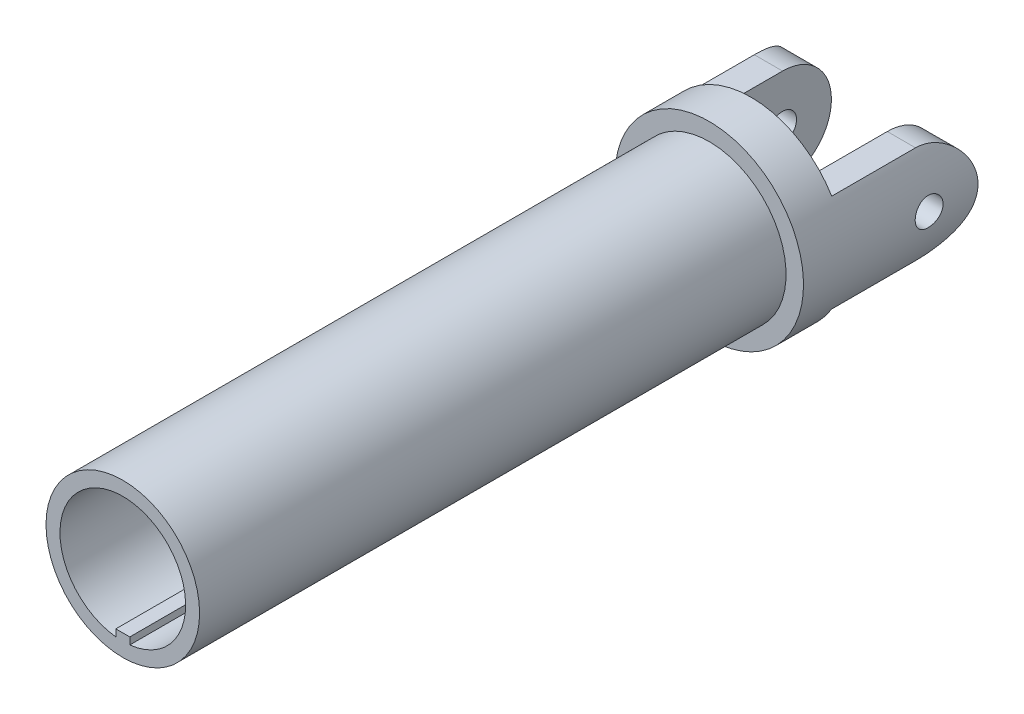
SolidWorks part; units mm, degrees
ref_plane "Front Plane" through (0, 0, 0) normal (0, 0, 1) x (1, 0, 0)
ref_plane "Top Plane" through (0, 0, 0) normal (0, 1, 0) x (1, 0, 0)
ref_plane "Right Plane" through (0, 0, 0) normal (1, 0, 0) x (0, 0, -1)
sketch "Sketch1" plane through (0, 0, 0) normal (0, 0, 1) x (1, 0, 0)
  circle A0 centre (0, 0) radius 5.5
  dimension "D1" = 11
extrude "Yoke" add sketch "Sketch1" along normal mid plane 42 contours A0
sketch "Sketch2" plane through (0, 0, -21) normal (0, 0, -1) x (-1, 0, 0)
  circle A0 centre (0, 0) radius 6.75
  dimension "D1" = 13.5
extrude "U Joint Base" add sketch "Sketch2" along normal blind 3
sketch "Sketch3" plane through (0, 0, -24) normal (0, 0, -1) x (-1, 0, 0)
  line L0 (-5.7717, 3.5) -> (-3.75, 3.5)
  line L1 (-3.75, 3.5) -> (-3.75, -3.5)
  line L2 (-3.75, -3.5) -> (-5.7717, -3.5)
  line L3 (3.75, -3.5) -> (3.75, 3.5)
  line L4 (3.75, 3.5) -> (5.7717, 3.5)
  line L5 (5.7717, -3.5) -> (3.75, -3.5)
  circle A0 centre (0, 0) radius 6.75 construction
  arc A1 (-5.7717, -3.5) -> (-5.7717, 3.5) centre (0, 0) cw
  arc A2 (5.7717, 3.5) -> (5.7717, -3.5) centre (0, 0) cw
  point P16 (0, 0)
  dimension "D2" = 7.5
  dimension "D3" = 7
  dimension "D1" = 2
extrude "U Joint Standups" add sketch "Sketch3" along normal blind 9.5
sketch "Sketch4" plane through (0, 0, 0) normal (1, 0, 0) x (0, 0, -1)
  line L0 (33.5, 3.5) -> (24, 3.5) construction
  line L1 (33.5, -3.5) -> (33.5, 3.5) construction
  line L2 (30, -3.5) -> (33.5, -3.5)
  line L3 (33.5, -3.5) -> (33.5, 0)
  line L4 (33.5, 0) -> (33.5, 3.5)
  line L5 (33.5, 3.5) -> (30, 3.5)
  line L6 (33.5, -3.5) -> (24, -3.5) construction
  arc A0 (33.5, 0) -> (30, 3.5) centre (30, 0) ccw
  arc A1 (30, -3.5) -> (33.5, 0) centre (30, 0) ccw
extrude "Standup Round" cut sketch "Sketch4" against normal through all both and the other way through all contours A1 L2 L3 | A0 L5 L4
sketch "Sketch5" plane through (0, 0, 0) normal (1, 0, 0) x (0, 0, -1)
  circle A0 centre (30, 0) radius 1
  dimension "D1" = 2
extrude "Ball Holes" cut sketch "Sketch5" against normal through all both and the other way through all
sketch "Sketch6" plane through (0, 0, 21) normal (0, 0, 1) x (1, 0, 0)
  line L0 (0.5, -4.4721) -> (0.5, -3.9721)
  line L1 (0.5, -3.9721) -> (-0.5, -3.9721)
  line L2 (-0.5, -3.9721) -> (-0.5, -4.4721)
  arc A0 (0.5, -4.4721) -> (-0.5, -4.4721) centre (0, 0) ccw
  dimension "D1" = 4.5
  dimension "D2" = 1
  dimension "D3" = 0.5
extrude "Keyway" cut sketch "Sketch6" against normal blind 42
